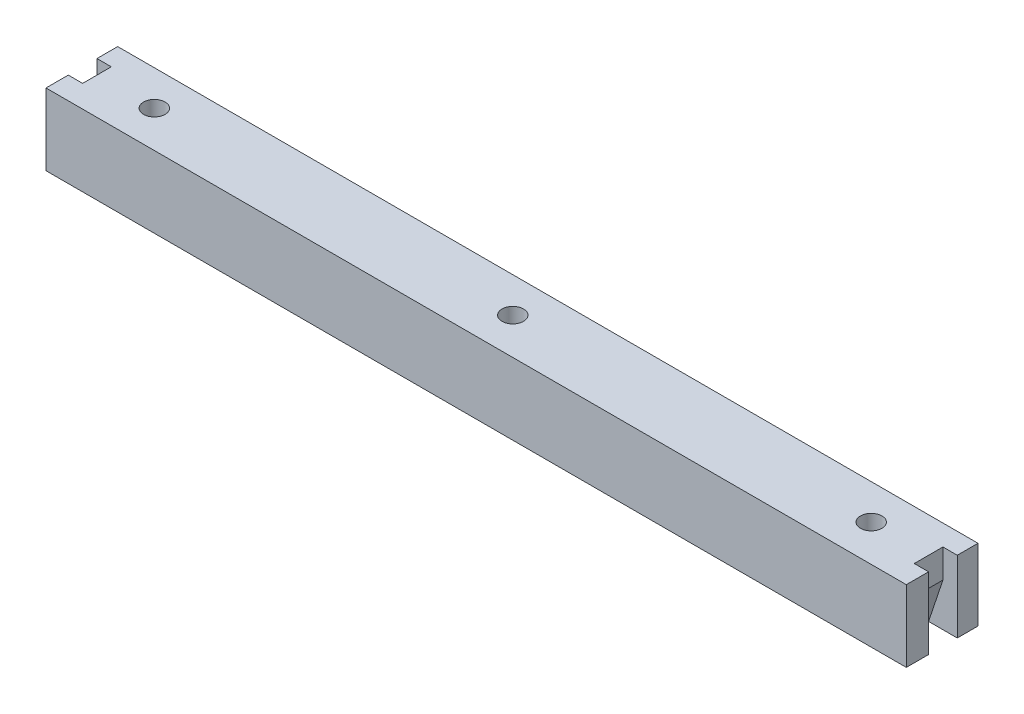
SolidWorks part; units mm, degrees
ref_plane "Plan de face" through (0, 0, 0) normal (0, 0, 1) x (1, 0, 0)
ref_plane "Plan de dessus" through (0, 0, 0) normal (0, 1, 0) x (1, 0, 0)
ref_plane "Plan de droite" through (0, 0, 0) normal (1, 0, 0) x (0, 0, -1)
sketch "Esquisse1" plane through (0, 0, 0) normal (0, 1, 0) x (1, 0, 0)
  line L1 (-60, 4.8921) -> (60, 4.8921)
  line L2 (-60, 4.8921) -> (-60, -5.1079)
  line L3 (-60, -5.1079) -> (60, -5.1079)
  line L4 (60, 4.8921) -> (60, -5.1079)
  circle A0 centre (-50, 0) radius 1.5
  circle A1 centre (0, 0) radius 1.5
  circle A2 centre (50, 0) radius 1.5
  dimension "D3" = 3
  dimension "D6" = 50
  dimension "D1" = 120
  dimension "D2" = 10
  dimension "D4" = 60
  dimension "D5" = 50
extrude "Boss.-Extru.1" add sketch "Esquisse1" along normal blind 10
sketch "Esquisse2" plane through (0, 0, 0) normal (0, 0, 1) x (1, 0, 0)
  line L0 (-58, 10) -> (-58, 6)
  line L1 (-60, 10) -> (60, 10) construction
  line L2 (-58, 6) -> (-56, 0)
  line L3 (-60, 0) -> (60, 0) construction
  line L4 (-56, 0) -> (-56, -10.8008)
  line L5 (-56, -10.8008) -> (-73.1532, -10.8008)
  line L6 (-73.1532, -10.8008) -> (-73.1532, 18.34)
  line L7 (-73.1532, 18.34) -> (-58, 18.34)
  line L8 (-58, 18.34) -> (-58, 10)
  line L9 (-60, 10) -> (-60, 0) construction
  line L10 (0, 0) -> (0, 28.7451) construction
  line L11 (58, 10) -> (58, 6)
  line L12 (56, 0) -> (56, -10.8008)
  line L13 (56, -10.8008) -> (73.1532, -10.8008)
  line L14 (73.1532, -10.8008) -> (73.1532, 18.34)
  line L15 (58, 6) -> (56, 0)
  line L16 (58, 18.34) -> (58, 10)
  line L17 (73.1532, 18.34) -> (58, 18.34)
  dimension "D1" = 2
  dimension "D2" = 4
  dimension "D3" = 4
extrude "Enlèv. mat.-Extru.1" cut sketch "Esquisse2" against normal blind 2 and the other way blind 2
